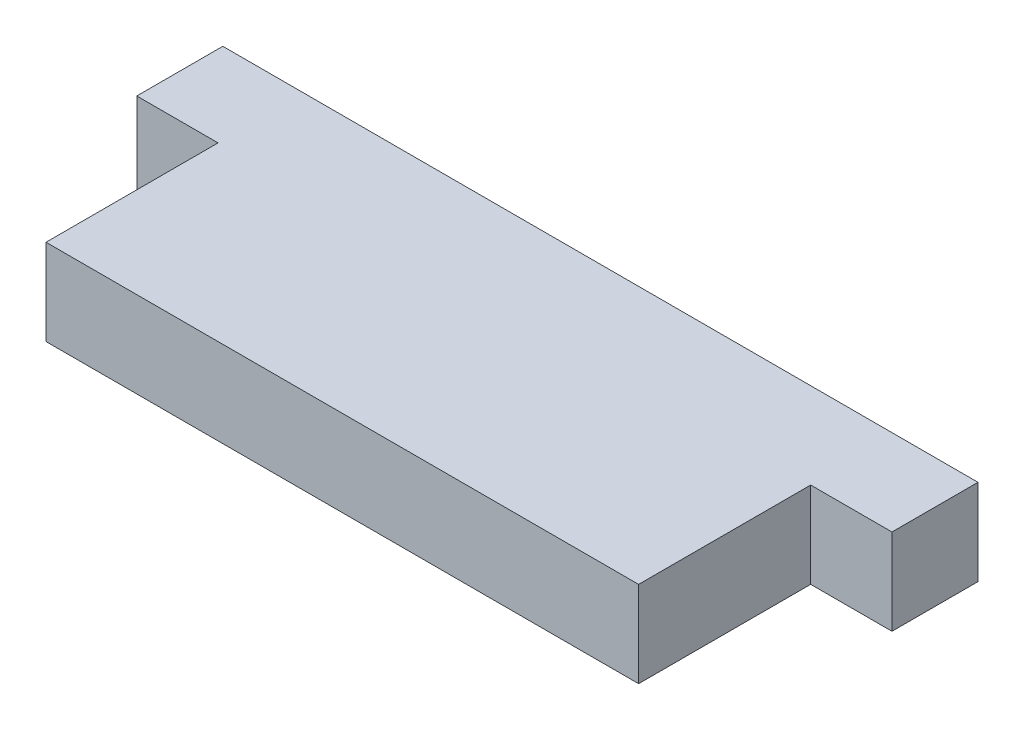
SolidWorks part; units mm, degrees
material "Beech"
ref_plane "Front Plane" through (0, 0, 0) normal (0, 0, 1) x (1, 0, 0)
ref_plane "Top Plane" through (0, 0, 0) normal (0, 1, 0) x (1, 0, 0)
ref_plane "Right Plane" through (0, 0, 0) normal (1, 0, 0) x (0, 0, -1)
sketch "Sketch1" plane through (0, 0, 0) normal (0, 1, 0) x (1, 0, 0)
  line L0 (0, 0) -> (0, 12.7)
  line L1 (0, 0) -> (43.74, 0)
  line L3 (43.74, 0) -> (43.74, 12.7)
  line L4 (-6, 19.05) -> (49.74, 19.05)
  line L5 (-6, 19.05) -> (-6, 12.7)
  line L6 (49.74, 19.05) -> (49.74, 12.7)
  line L7 (-6, 12.7) -> (0, 12.7)
  line L8 (43.74, 12.7) -> (49.74, 12.7)
  dimension "D1" = 12.7
  dimension "D2" = 43.74
  dimension "D3" = 6.35
  dimension "D4" = 6
  dimension "D5" = 6
extrude "Boss-Extrude1" add sketch "Sketch1" along normal blind 6.35
equation "\"MotorMountLegLength\"=.25in"
equation "\"GearOffset\"=.264907in"
equation "\"D4@Sketch1\"=\"TriggerRackOffset\""
equation "\"D5@Sketch1\"=\"TriggerRackOffset\""
equation "\"D2@Sketch1\" = \"CageLeftBottomEdge\" + \"CageRightBottomEdge\""
equation "\"CageLeftBottomEdge\"=22.11mm"
equation "\"CageLeftTopEdge\"=22.11mm"
equation "\"CageRightBottomEdge\"=21.63mm"
equation "\"CageRightTopEdge\"=21.63mm"
equation "\"CageHeight\"=86.04mm"
equation "\"CageLength\"=73.76mm"
equation "\"CageTopScrewClearance\"=10mm"
equation "\"CageBottomScrewClearance\"=25mm"
equation "\"CageLeftTopDepth\"= 11.65mm"
equation "\"CageLeftBottomDepth\"=11.11mm"
equation "\"CageLeftTopHeight\"=8.56175mm"
equation "\"CageLeftBottomHeight\"=16mm"
equation "\"CageRightTopDepth\"= 11.05mm"
equation "\"CageRightBottomDepth\"=10.58mm"
equation "\"CageRightTopHeight\"=9.6mm"
equation "\"CageRightBottomHeight\"=15.49mm"
equation "\"CageLeftTopChannelDepth\"=2.41908mm"
equation "\"CageLeftBottomChannelDepth\"=2.588mm"
equation "\"CageLeftChannelHeight\"=11.7mm"
equation "\"CageRightTopChannelDepth\"=2.32mm"
equation "\"CageRightBottomChannelDepth\"=2.318mm"
equation "\"CageRightChannelHeight\"=10mm"
equation "\"CageChanRelHeight\"=23.99mm"
equation "\"CageChanRelDepth\"=5.492mm"
equation "\"CageChamberRadius\"=16.261mm"
equation "\"CageScrewDiameter\"=4.8mm"
equation "\"CageSetScrewDiameter\"=3.5mm"
equation "\"CageAxleRadius\"=6.639mm"
equation "\"CageAxleKeyHeight\"=1.619mm"
equation "\"CageAxleKeyWidth\"=2.662mm"
equation "\"CageHoseWindowWidth\"=16.29mm"
equation "\"CageHoseWindowHeight\"=26.5mm"
equation "\"CageHoseWindow-Edge\"=8.89mm"
equation "\"CageScrew-VerticalEdge\"=5.0mm"
equation "\"CageScrew-HorizontalEdge\"=7.5mm"
equation "\"CageScrew-HoseCornerScrewEdge\"=4.45mm"
equation "\"CageAxle-BottomEdge\"=56.05mm"
equation "\"CageAxle-FrontEdge\"=46.03mm"
equation "\"CageBackSetScrew-Axle\"=40mm"
equation "\"CageFrontSetScrew-Axle\"=22mm"
equation "\"CageVelocityWindow-BackEdge\"=34.8mm"
equation "\"CageVelocityWindow-BottomEdge\"=27.55mm"
equation "\"CageVelocityWindowHeight\"=22.29mm"
equation "\"CageVelocityWindowWidth\"=12.61mm"
equation "\"TriggerSlot-BottomEdge\"=6.35mm"
equation "\"TriggerSlot-FrontEdge\"=15mm"
equation "\"TriggerSlotSize\"=6.7mm"
equation "\"TriggerRackOffset\"=6mm"
equation "\"TriggerSlotSizeInt\"=.25in"
equation "\"TriggerSlotSpacing\"=.25in"
equation "\"TriggerMiniSlotWidth\"=3.5mm"
equation "\"TriggerRackWidth\"=6.5mm"
equation "\"pandiscradius\"=14in"
equation "\"towermaterialwidth\"=.25in"
equation "\"towerslotlength\"=.5in"
equation "\"towermarkerspace\"=5in"
equation "\"towerslothorizoffset\"=1in"
equation "\"towerslothorizspacing\"=2in"
equation "\"towerslotvertoffset\"=3in"
equation "\"towerslotvertspacing\"=1in"
equation "\"towerheight\"=12in"
equation "\"towerupslot\"=1in"
equation "\"toweraxle\"=.5in"
equation "\"stepperouterrad\"=10mm"
equation "\"stepperscrewsize\"=3.45mm"
equation "\"stepperscrewc2c\"=49.5mm"
equation "\"stepperdepthoffset\"=24mm"
equation "\"stepperhorizoffset\"=22.91mm"
equation "\"shaftslotOD\"=18.8mm"
equation "\"shaftslotID\"=13.28mm"
equation "\"shaftkeywidth\"=2.67mm"
equation "\"shaftkeydepth\"=1.8mm"
equation "\"shaftcollartotaldepth\"=9.71mm"
equation "\"shaftsquaredepth\"=6mm"
equation "\"shaftsetscrewsize\"=3.5mm"
equation "\"shaftkeytightdepth\"=1.85mm"
equation "\"shaftslottightID\"=12.78mm"
equation "\"shaftsetscrewoffset\"=9mm"
equation "\"cagecollartotaldepth\"=20mm"
equation "\"cagecollartotalwidth\"=35mm"
equation "\"cagecollarbasedepth\"=4mm"
equation "\"gearhubintdiam\"=30mm"
equation "\"gearhubintwid\"=12.21mm"
equation "\"towerspeedwidth\"=2in"
equation "\"towerspeedheight\"=8in"
equation "\"towerspeedgap\"=2in"
equation "\"stepperaxleflat\"=.037in"
equation "\"stepperaxlerad\"=0.11811024in"
equation "\"ajaxaxlesize\"=3.87mm"
equation "\"ajaxinnercut\"=2.3mm"
equation "\"ajaxwidth\"=6.1mm"
equation "\"ajaxdiametral\"=25.8854"
equation "\"ajaxcutoutdepth\"=2.3mm"
equation "\"ajax4020gap\"=29.5mm"
equation "\"ajax4010gap\"=24.5mm"
equation "\"ajax20hubbuffer\"=6.1mm"
equation "\"ajax20hubholeoffset\"=.19685in"
equation "\"ajax20hubholesize\"=.059055in"
equation "\"ajax20cutoutint\"=13.4mm"
equation "\"ajax40hubholesize\"=7.21mm"
equation "\"ajax40hubholeoffset\"=10mm"
equation "\"ajax40hubbuffer\"=8.9mm"
equation "\"ajax40cutoutint\"=32.6mm"
equation "\"bearingpandiscrad\"=6.8in"
equation "\"bearingpandiscang\"=48.75deg"
equation "\"bearingclearholedist\"=4.7345in"
equation "\"bearingclearholesize\"=.5in"
equation "\"bearingclearholeang\"=22.5deg"
equation "\"bearingmountholedist\"=4.25in"
equation "\"bearingwirehole\"=1.5in"
equation "\"no6diam\"=.146in"
equation "\"shortconangle\"=20deg"
equation "\"shortconlen\"=.875in"
equation "\"longconlen\"=1.25in"
equation "\"longconangle\"=15deg"
